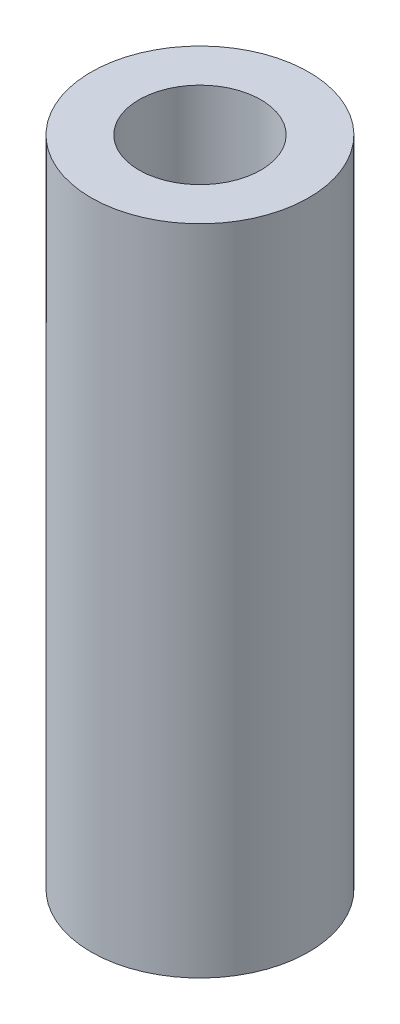
SolidWorks part; units mm, degrees
ref_plane "Front Plane" through (0, 0, 0) normal (0, 0, 1) x (1, 0, 0)
ref_plane "Top Plane" through (0, 0, 0) normal (0, 1, 0) x (1, 0, 0)
ref_plane "Right Plane" through (0, 0, 0) normal (1, 0, 0) x (0, 0, -1)
sketch "Sketch1" plane through (0, 0, 0) normal (0, 1, 0) x (1, 0, 0)
  circle A0 centre (0, 0) radius 2.5
  circle A1 centre (0, 0) radius 1.4
  dimension "D1" = 5
  dimension "D2" = 2.8
extrude "Boss-Extrude1" add sketch "Sketch1" along normal blind 15
